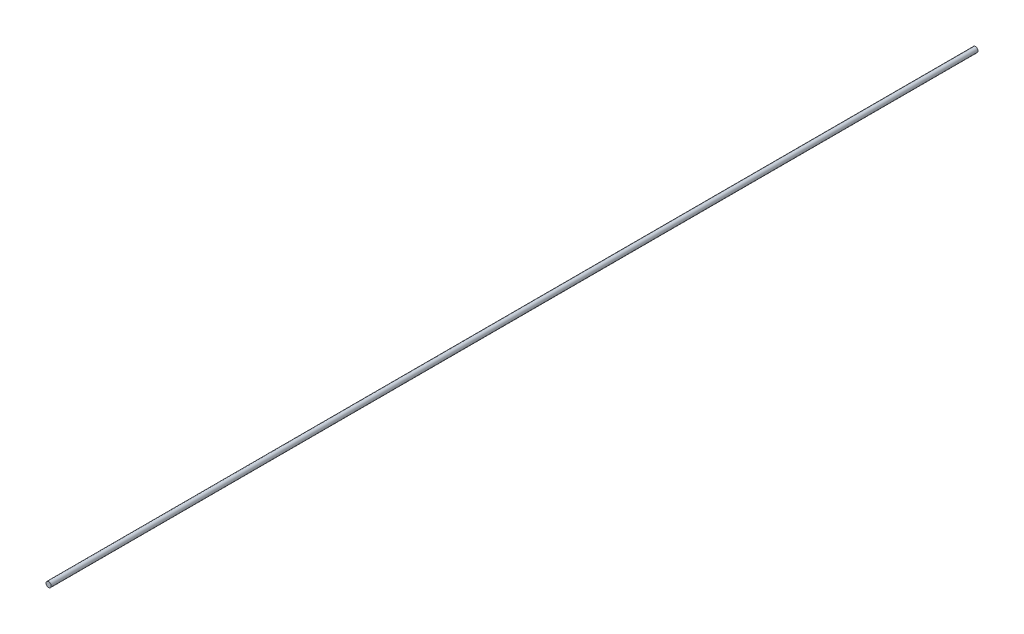
SolidWorks part; units mm, degrees
material "Liga de aço (SS)"
ref_plane "Plano frontal" through (0, 0, 0) normal (0, 0, 1) x (1, 0, 0)
ref_plane "Plano superior" through (0, 0, 0) normal (0, 1, 0) x (1, 0, 0)
ref_plane "Plano direito" through (0, 0, 0) normal (1, 0, 0) x (0, 0, -1)
ref_plane "Plano1" through (0, 0, 0) normal (0, -1, 0) x (1, 0, 0)
sketch "Esboço1" plane through (0, 0, 0) normal (0, -1, 0) x (1, 0, 0)
  line L0 (5, 1800) -> (0, 1800)
  line L1 (0, 1800) -> (0, 0)
  line L2 (0, 0) -> (5, 0)
  line L3 (5, 0) -> (5, 1800)
  line L4 (0, 1800) -> (0, 0) construction
  dimension "D1" = 5
  dimension "D2" = 1800
revolve "Revolução1" add sketch "Esboço1" angle 360 about L4
